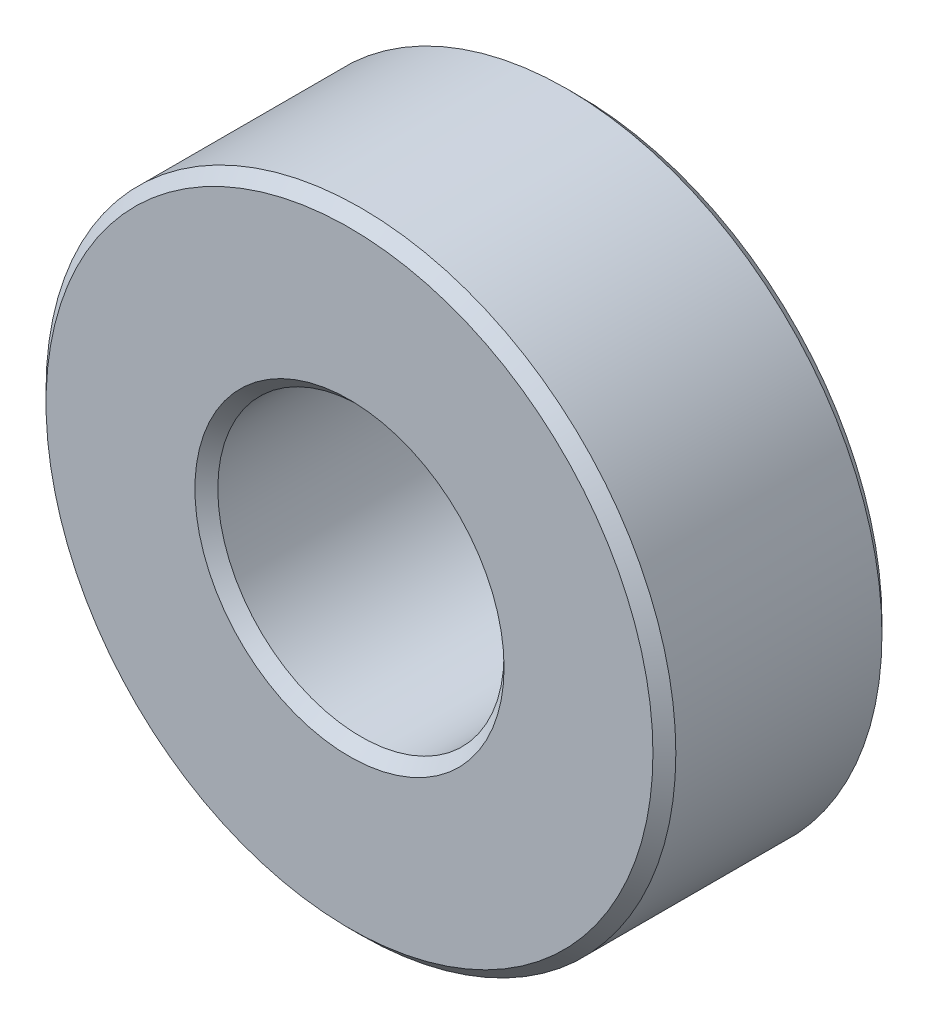
SolidWorks part; units mm, degrees
material "Plain Carbon Steel"
ref_plane "Front Plane" through (0, 0, 0) normal (0, 0, 1) x (1, 0, 0)
ref_plane "Top Plane" through (0, 0, 0) normal (0, 1, 0) x (1, 0, 0)
ref_plane "Right Plane" through (0, 0, 0) normal (1, 0, 0) x (0, 0, -1)
sketch "Sketch1" plane through (0, 0, 0) normal (0, 0, 1) x (1, 0, 0)
  circle A0 centre (0, 0) radius 2.5
  circle A1 centre (0, 0) radius 5.5
  dimension "D1" = 5
  dimension "D2" = 11
extrude "Boss-Extrude1" add sketch "Sketch1" along normal blind 4
chamfer "Chamfer1" distance 0.2 angle 45 4 edges at (2.5, 0, 0) (5.5, 0, 0) (2.5, 0, 4) (5.5, 0, 4)
